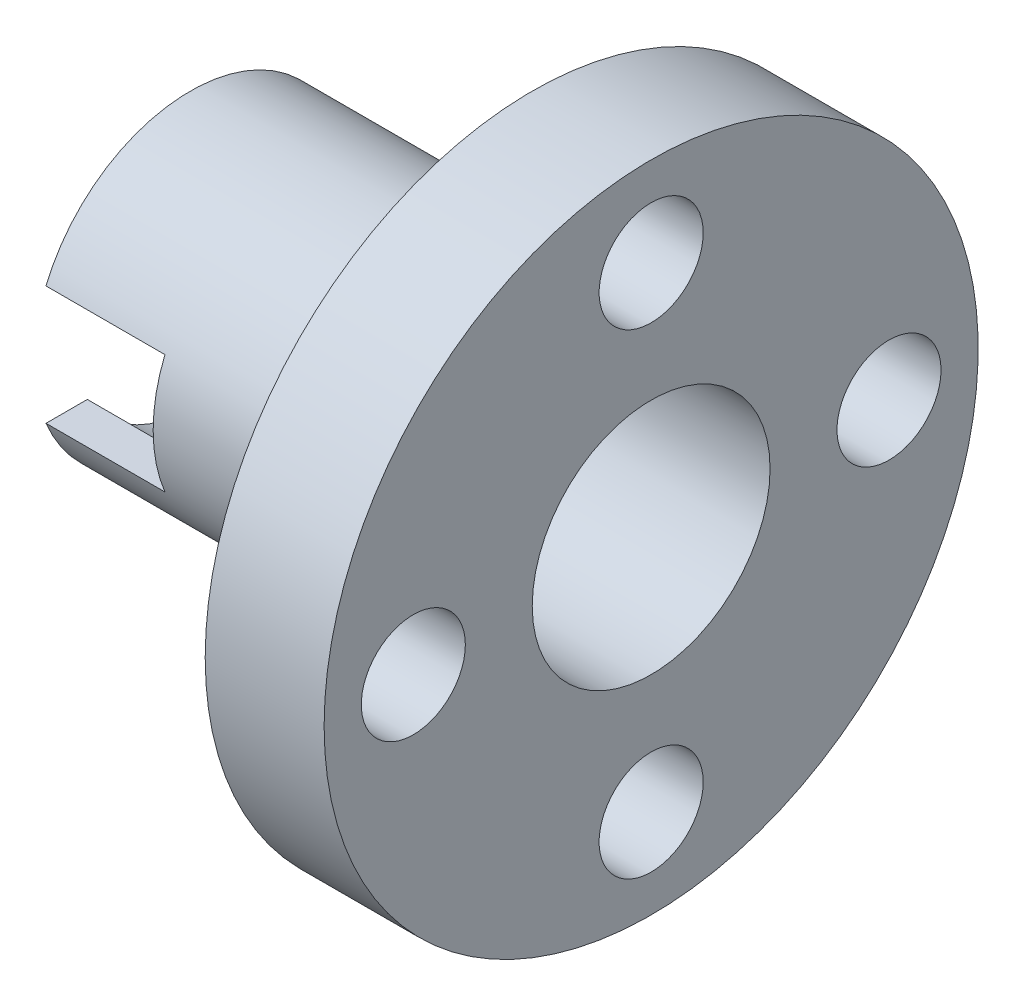
SolidWorks part; units mm, degrees
ref_plane "Front Plane" through (0, 0, 0) normal (0, 0, 1) x (1, 0, 0)
ref_plane "Top Plane" through (0, 0, 0) normal (0, 1, 0) x (1, 0, 0)
ref_plane "Right Plane" through (0, 0, 0) normal (1, 0, 0) x (0, 0, -1)
sketch "Sketch1" plane through (0, 0, 0) normal (0, 1, 0) x (1, 0, 0)
  line L0 (-43.7073, 0) -> (55.2195, 0) construction
  line L1 (-15.5, 4) -> (-15.5, 5.25)
  line L2 (-15.5, 5.25) -> (-4, 5.25)
  line L3 (-4, 5.25) -> (-4, 11)
  line L4 (-4, 11) -> (0, 11)
  line L6 (0, 4) -> (-15.5, 4)
  line L7 (0, 11) -> (0, 4)
  dimension "D1" = 4
  dimension "D2" = 5.25
  dimension "D3" = 4
  dimension "D4" = 11.5
  dimension "D5" = 11
revolve "Revolve1" add sketch "Sketch1" angle 360 about L0
sketch "Sketch2" plane through (0, 0, 0) normal (1, 0, 0) x (0, 0, -1)
  circle A0 centre (0, 0) radius 8 construction
  circle A1 centre (0, 8) radius 1.75
  circle A2 centre (8, 0) radius 1.75
  circle A3 centre (0, -8) radius 1.75
  circle A4 centre (-8, 0) radius 1.75
  dimension "D1" = 16
  dimension "D2" = 3.5
extrude "Cut-Extrude1" cut sketch "Sketch2" against normal up to next
sketch "Sketch3" plane through (0, 0, 0) normal (0, 0, 1) x (1, 0, 0)
  line L0 (-15.5, 5.25) -> (-15.5, -5.25) construction
  line L1 (-15.5, 2) -> (-11.5, 2)
  line L2 (-15.5, 2) -> (-15.5, -2)
  line L3 (-15.5, -2) -> (-11.5, -2)
  line L4 (-11.5, 2) -> (-11.5, -2)
  point P6 (-15.5, 0)
  dimension "D1" = 4
extrude "Cut-Extrude2" cut sketch "Sketch3" against normal through all both and the other way through all
